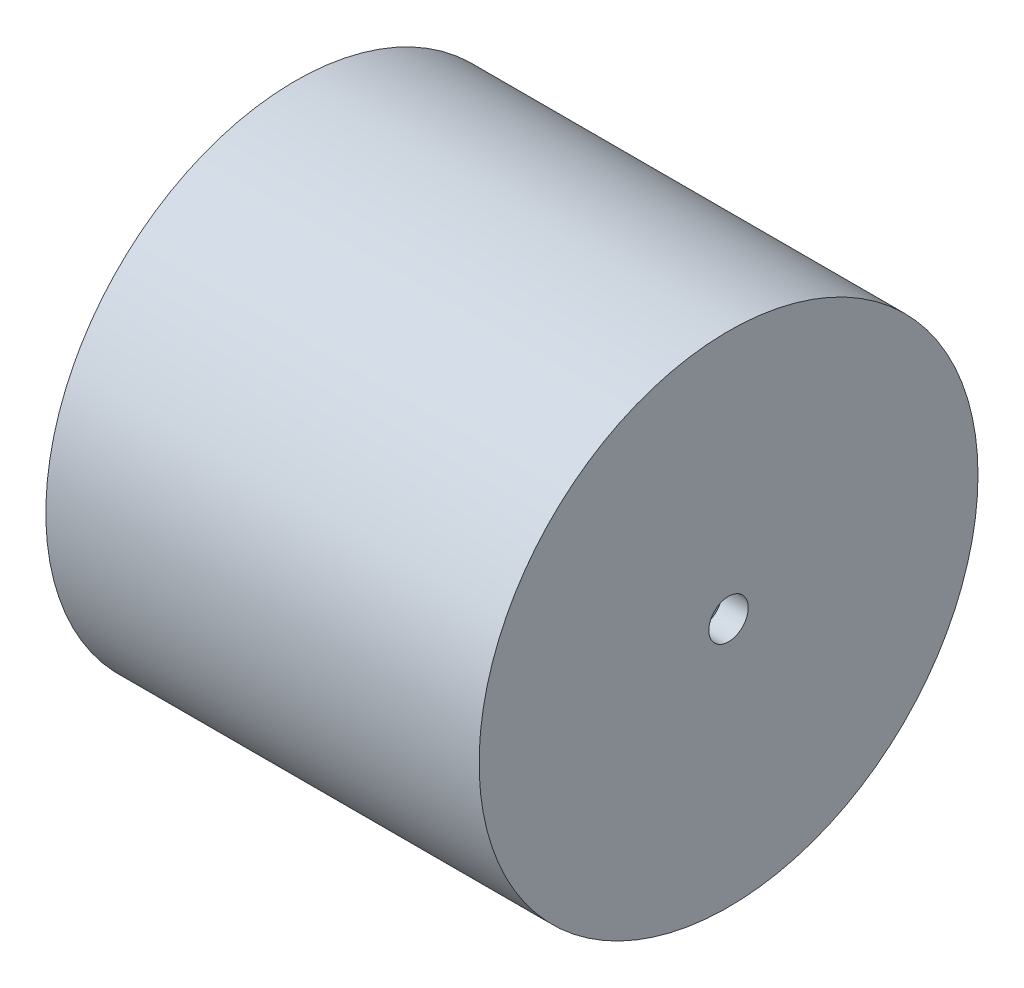
SolidWorks part; units mm, degrees
ref_plane "Front Plane" through (0, 0, 0) normal (0, 0, 1) x (1, 0, 0)
ref_plane "Top Plane" through (0, 0, 0) normal (0, 1, 0) x (1, 0, 0)
ref_plane "Right Plane" through (0, 0, 0) normal (1, 0, 0) x (0, 0, -1)
sketch "Sketch1" plane through (0, 0, 0) normal (1, 0, 0) x (0, 0, -1)
  circle A0 centre (0, 0) radius 19
  dimension "D1" = 38
extrude "Boss-Extrude1" add sketch "Sketch1" along normal blind 33
sketch "Sketch2" plane through (33, 0, 0) normal (1, 0, 0) x (0, 0, -1)
  circle A0 centre (0, 0) radius 1.5
  dimension "D1" = 3
extrude "Cut-Extrude1" cut sketch "Sketch2" against normal blind 2
